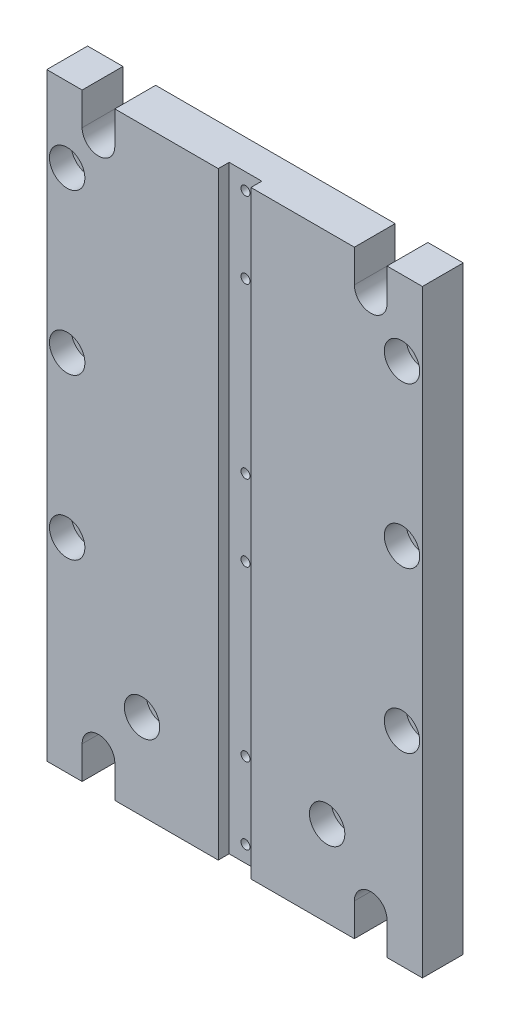
SolidWorks part; units mm, degrees
ref_plane "Alzado" through (0, 0, 0) normal (0, 0, 1) x (1, 0, 0)
ref_plane "Planta" through (0, 0, 0) normal (0, 1, 0) x (1, 0, 0)
ref_plane "Vista lateral" through (0, 0, 0) normal (1, 0, 0) x (0, 0, -1)
sketch "Croquis1" plane through (0, 0, 0) normal (0, 0, 1) x (1, 0, 0)
  line L1 (69, -110) -> (-69, -110)
  line L2 (69, -110) -> (69, 110)
  line L3 (69, 110) -> (-69, 110)
  line L4 (-69, -110) -> (-69, 110)
  line L5 (69, -110) -> (-69, 110) construction
  line L6 (69, 110) -> (-69, -110) construction
  point P0 (0, 0)
  dimension "D1" = 220
  dimension "D2" = 138
extrude "Saliente-Extruir1" add sketch "Croquis1" along normal blind 15
sketch "Croquis2" plane through (0, 0, 15) normal (0, 0, 1) x (1, 0, 0)
  line L0 (-50, 98) -> (-50, -98) construction
  line L1 (50, 98) -> (50, -98) construction
  line L2 (0, 124.1927) -> (0, -126.652) construction
  line L3 (69, 110) -> (-69, 110) construction
  line L4 (-69, -110) -> (69, -110) construction
  line L5 (-56, 122.8919) -> (-56, 98)
  line L6 (-44, 122.8919) -> (-44, 98)
  line L7 (44, 116.9098) -> (44, 98)
  line L8 (56, 116.9098) -> (56, 98)
  line L9 (44, -98) -> (44, -115.8307)
  line L10 (56, -98) -> (56, -115.8307)
  line L11 (-56, -98) -> (-56, -115.8861)
  line L12 (-44, -98) -> (-44, -115.8861)
  line L13 (-56, 122.8919) -> (-44, 122.8919)
  line L14 (44, 116.9098) -> (56, 116.9098)
  line L15 (-56, -115.8861) -> (-44, -115.8861)
  line L16 (44, -115.8307) -> (56, -115.8307)
  arc A0 (-56, 98) -> (-44, 98) centre (-50, 98) ccw
  arc A1 (44, 98) -> (56, 98) centre (50, 98) ccw
  arc A2 (56, -98) -> (44, -98) centre (50, -98) ccw
  arc A3 (-44, -98) -> (-56, -98) centre (-50, -98) ccw
  dimension "D5" = 12
  dimension "D1" = 50
  dimension "D2" = 50
  dimension "D3" = 12
  dimension "D4" = 12
extrude "Cortar-Extruir1" cut sketch "Croquis2" against normal blind 76.5
sketch "Croquis3" plane through (0, 0, 15) normal (0, 0, 1) x (1, 0, 0)
  line L0 (0, 117.9811) -> (0, -122.8903) construction
  line L1 (-69, 110) -> (-69, -110) construction
  line L2 (-56, 110) -> (-69, 110) construction
  line L3 (-44, -110) -> (44, -110) construction
  circle A0 centre (-61.5, 82.5) radius 4.25
  circle A1 centre (-61.5, 23.7) radius 4.25
  circle A2 centre (-61.5, -35.1) radius 4.25
  circle A3 centre (-34, -78.5) radius 4.25
  circle A4 centre (34, -78.5) radius 4.25
  circle A5 centre (61.5, -35.1) radius 4.25
  circle A6 centre (61.5, 23.7) radius 4.25
  circle A7 centre (61.5, 82.5) radius 4.25
  point P13 (-62.5, 110)
  dimension "D1" = 8.5
  dimension "D2" = 7.5
  dimension "D3" = 27.5
  dimension "D4" = 58.8
  dimension "D5" = 58.8
  dimension "D6" = 31.5
  dimension "D7" = 35
  dimension "D8" = 34
  dimension "D9" = 43.4
extrude "Cortar-Extruir2" cut sketch "Croquis3" against normal blind 76.5
sketch "Croquis4" plane through (0, 0, 15) normal (0, 0, 1) x (1, 0, 0)
  circle A0 centre (-61.5, 82.5) radius 6.5
  circle A1 centre (-61.5, 23.7) radius 6.5
  circle A2 centre (-61.5, -35.1) radius 6.5
  circle A3 centre (-34, -78.5) radius 6.5
  circle A4 centre (61.5, -35.1) radius 6.5
  circle A5 centre (61.5, 23.7) radius 6.5
  circle A6 centre (61.5, 82.5) radius 6.5
  circle A7 centre (34, -78.5) radius 6.5
  dimension "D1" = 13
extrude "Cortar-Extruir3" cut sketch "Croquis4" against normal blind 8
sketch "Croquis5" plane through (0, 0, 15) normal (0, 0, 1) x (1, 0, 0)
  line L0 (44, 110) -> (-44, 110) construction
  line L1 (6, -110) -> (-6, -110)
  line L2 (6, -110) -> (6, 110)
  line L3 (6, 110) -> (-6, 110)
  line L4 (-6, -110) -> (-6, 110)
  line L5 (6, -110) -> (-6, 110) construction
  line L6 (6, 110) -> (-6, -110) construction
  point P0 (0, 0)
  dimension "D1" = 12
extrude "Cortar-Extruir4" cut sketch "Croquis5" against normal blind 4
hole_wizard "Taladro roscado M41" positions "Croquis7" profile "Croquis6" tap size "M4" standard "DIN"
sketch "Croquis7" plane through (0, 0, 11) normal (0, 0, 1) x (1, 0, 0)
  line L0 (-6, -110) -> (6, -110) construction
  line L1 (6, 110) -> (-6, 110) construction
  point P0 (0, 104)
  point P1 (0, 76)
  point P3 (0, 14)
  point P5 (0, -14)
  point P7 (0, -76)
  point P9 (0, -104)
  point P12 (0, -110)
  point P15 (0, 110)
  dimension "D1" = 6
  dimension "D2" = 28
  dimension "D3" = 62
  dimension "D4" = 28
  dimension "D5" = 62
  dimension "D6" = 28
  dimension "D7" = 6
sketch "Croquis6" plane through (0, 104, 11) normal (1, 0, 0) x (0, -1, 0)
  line L0 (0, 0) -> (0, 8.9914)
  line L1 (0, 8.9914) -> (1.65, 8)
  line L2 (1.65, 8) -> (1.65, 0)
  line L5 (1.65, 0) -> (0, 0)
  line L10 (0, 8.9914) -> (-1.65, 8) construction
  line L11 (0, -6.35) -> (0, 107.95) construction
  dimension "Diámetro de perforador para roscar" = 3.3
  dimension "Profundidad de perforador para roscar" = 8
  dimension "Ángulo de perforador" = 118
cosmetic thread "Rosca de taladro1" parameters "D1"=8, "D2"=4
cosmetic thread "Rosca de taladro2" parameters "D1"=8, "D2"=4
cosmetic thread "Rosca de taladro3" parameters "D1"=8, "D2"=4
cosmetic thread "Rosca de taladro4" parameters "D1"=8, "D2"=4
cosmetic thread "Rosca de taladro5" parameters "D1"=8, "D2"=4
cosmetic thread "Rosca de taladro6" parameters "D1"=8, "D2"=4
sketch "Croquis8" plane through (0, 0, 0) normal (0, 0, -1) x (-1, 0, 0)
  line L0 (0, 116.2001) -> (0, -121.5285) construction
  line L1 (44, -110) -> (-44, -110) construction
  line L2 (-44, 110) -> (44, 110) construction
  line L3 (30, -55.5) -> (-30, -55.5)
  line L4 (36, -49.5) -> (36, 66.5)
  line L6 (30, 72.5) -> (-30, 72.5)
  line L7 (-36, -49.5) -> (-36, 66.5)
  arc A0 (30, -55.5) -> (36, -49.5) centre (30, -49.5) ccw
  arc A1 (36, 66.5) -> (30, 72.5) centre (30, 66.5) ccw
  arc A2 (-36, 66.5) -> (-30, 72.5) centre (-30, 66.5) cw
  arc A3 (-30, -55.5) -> (-36, -49.5) centre (-30, -49.5) cw
  point P3 (0, 72.5)
  point P21 (0, -55.5)
  dimension "D1" = 12
  dimension "D2" = 60.5
  dimension "D3" = 116
  dimension "D4" = 43.5
  dimension "D5" = 60
extrude "Cortar-Extruir5" cut sketch "Croquis8" against normal blind 8
chamfer "Chaflán1" distance 2 angle 45 8 edges at (36, 8.5, 0) (34.2426, -53.7426, 0) (34.2426, 70.7426, 0) (0, -55.5, 0) (0, 72.5, 0) (-34.2426, -53.7426, 0) (-34.2426, 70.7426, 0) (-36, 8.5, 0)
